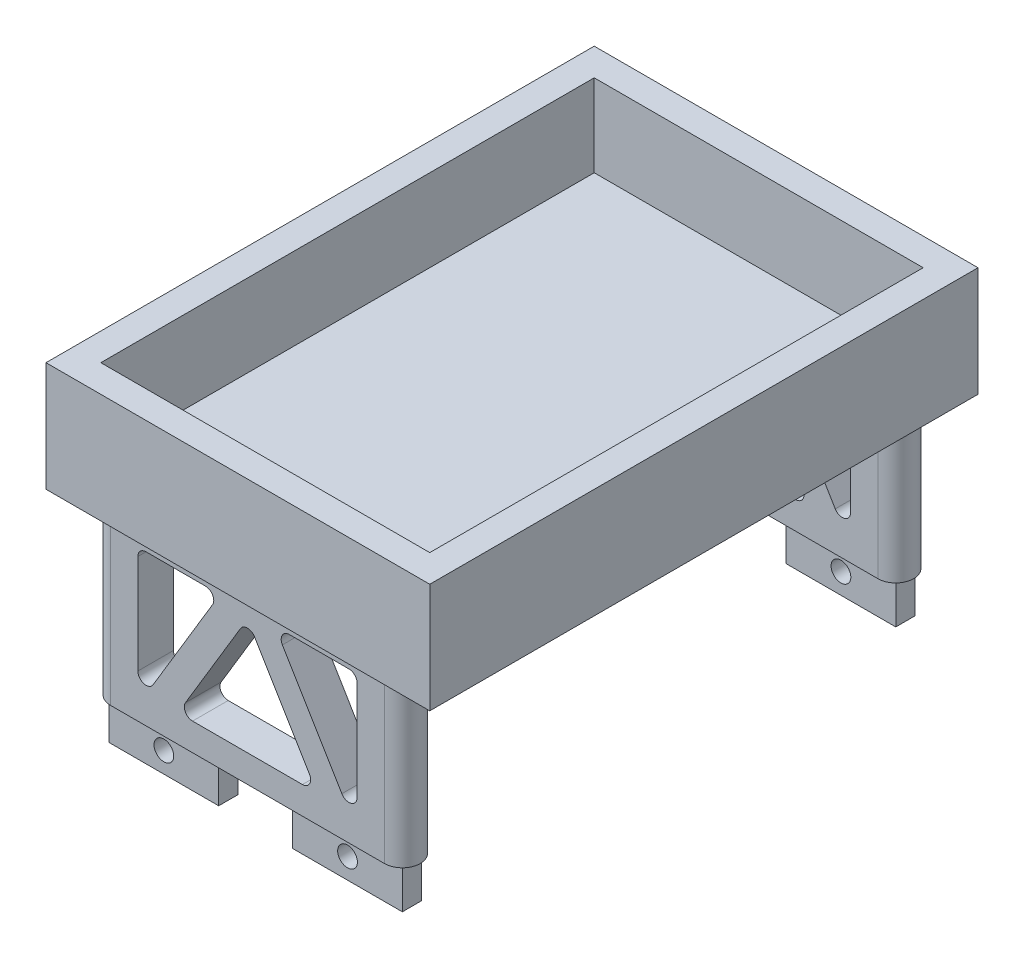
SolidWorks part; units mm, degrees
ref_plane "Front Plane" through (0, 0, 0) normal (0, 0, 1) x (1, 0, 0)
ref_plane "Top Plane" through (0, 0, 0) normal (0, 1, 0) x (1, 0, 0)
ref_plane "Right Plane" through (0, 0, 0) normal (1, 0, 0) x (0, 0, -1)
sketch "Sketch1" plane through (0, 0, 0) normal (0, 1, 0) x (1, 0, 0)
  line L0 (-52.3842, 23.5477) -> (-52.3842, -66.4523) construction
  line L1 (-2.3842, 23.5477) -> (-2.3842, -66.4523) construction
  line L2 (-52.3842, 23.5477) -> (-2.3842, 23.5477) construction
  line L3 (-52.3842, -21.4523) -> (-2.3842, -21.4523) construction
  line L4 (-54.1342, 25.2977) -> (-34.1342, 25.2977)
  line L5 (-54.1342, 25.2977) -> (-54.1342, 21.7977)
  line L6 (-54.1342, 21.7977) -> (-34.1342, 21.7977)
  line L7 (-34.1342, 25.2977) -> (-34.1342, 21.7977)
  line L8 (-0.6342, 25.2977) -> (-20.6342, 25.2977)
  line L9 (-0.6342, 25.2977) -> (-0.6342, 21.7977)
  line L10 (-0.6342, 21.7977) -> (-20.6342, 21.7977)
  line L11 (-20.6342, 25.2977) -> (-20.6342, 21.7977)
  line L13 (-54.1342, -68.2023) -> (-34.1342, -68.2023)
  line L14 (-54.1342, -68.2023) -> (-54.1342, -64.7023)
  line L15 (-54.1342, -64.7023) -> (-34.1342, -64.7023)
  line L16 (-34.1342, -68.2023) -> (-34.1342, -64.7023)
  line L17 (-0.6342, -68.2023) -> (-20.6342, -68.2023)
  line L18 (-0.6342, -68.2023) -> (-0.6342, -64.7023)
  line L19 (-0.6342, -64.7023) -> (-20.6342, -64.7023)
  line L20 (-20.6342, -68.2023) -> (-20.6342, -64.7023)
  circle A0 centre (-52.3842, 23.5477) radius 1.75 construction
  circle A1 centre (-2.3842, 23.5477) radius 1.75 construction
  circle A2 centre (-52.3842, -66.4523) radius 1.75 construction
  circle A3 centre (-2.3842, -66.4523) radius 1.75 construction
  point P29 (-52.3842, 23.5477)
  point P30 (-2.3842, 23.5477)
  point P31 (-52.3842, -66.4523)
  point P32 (-2.3842, -66.4523)
  dimension "D1" = 3.5
  dimension "D3" = 90
  dimension "D2" = 50
  dimension "D4" = 20
extrude "Boss-Extrude1" add sketch "Sketch1" along normal blind 7.5
sketch "Sketch2" plane through (0, 7.5, 0) normal (0, 1, 0) x (1, 0, 0)
  line L1 (-34.1342, 25.2977) -> (-54.1342, 25.2977) construction
  line L2 (-54.1342, 25.2977) -> (-54.1342, 21.7977) construction
  line L3 (-0.6342, 21.7977) -> (-0.6342, 25.2977) construction
  line L5 (-0.6342, 25.2977) -> (-20.6342, 25.2977) construction
  line L8 (-34.1342, -64.7023) -> (-54.1342, -64.7023) construction
  line L9 (-54.1342, -64.7023) -> (-54.1342, -68.2023) construction
  line L10 (-0.6342, -64.7023) -> (-20.6342, -64.7023) construction
  line L11 (-0.6342, -68.2023) -> (-0.6342, -64.7023) construction
  circle A0 centre (-52.3842, -66.4523) radius 3.25 construction
  circle A1 centre (-52.3842, 23.5477) radius 3.25 construction
  circle A2 centre (-2.3842, 23.5477) radius 3.25 construction
  circle A3 centre (-2.3842, -66.4523) radius 3.25
  circle A4 centre (-52.3842, 23.5477) radius 3.25
  circle A5 centre (-2.3842, 23.5477) radius 3.25
  circle A6 centre (-52.3842, -66.4523) radius 3.25
  point P31 (2.0333, -67.0433)
  dimension "D1" = 6.5
  dimension "D2" = 1.75
  dimension "D3" = 1.75
  dimension "D4" = 1.75
  dimension "D5" = 1.75
  dimension "D6" = 1.75
  dimension "D7" = 1.75
  dimension "D8" = 1.75
  dimension "D9" = 1.75
extrude "Boss-Extrude2" add sketch "Sketch2" along normal blind 30
sketch "Sketch3" plane through (0, 37.5, 0) normal (0, 1, 0) x (1, 0, 0)
  line L1 (-62.3842, 28.5477) -> (7.6158, 28.5477)
  line L2 (-62.3842, 28.5477) -> (-62.3842, -71.4523)
  line L3 (-62.3842, -71.4523) -> (7.6158, -71.4523)
  line L4 (7.6158, 28.5477) -> (7.6158, -71.4523)
  circle A3 centre (-52.3842, 23.5477) radius 3.25 construction
  circle A4 centre (-2.3842, 23.5477) radius 3.25 construction
  circle A5 centre (-2.3842, -66.4523) radius 3.25 construction
  dimension "D1" = 10
  dimension "D2" = 5
  dimension "D3" = 5
  dimension "D4" = 10
extrude "Boss-Extrude3" add sketch "Sketch3" along normal blind 20
sketch "Sketch4" plane through (0, 57.5, 0) normal (0, 1, 0) x (1, 0, 0)
  line L0 (7.6158, 28.5477) -> (-62.3842, 28.5477) construction
  line L1 (-57.3842, 23.5477) -> (2.6158, 23.5477)
  line L2 (-57.3842, 23.5477) -> (-57.3842, -66.4523)
  line L3 (-57.3842, -66.4523) -> (2.6158, -66.4523)
  line L4 (2.6158, 23.5477) -> (2.6158, -66.4523)
  line L5 (7.6158, -71.4523) -> (7.6158, 28.5477) construction
  line L6 (-62.3842, -71.4523) -> (7.6158, -71.4523) construction
  line L7 (-62.3842, 28.5477) -> (-62.3842, -71.4523) construction
  dimension "D1" = 5
  dimension "D2" = 5
  dimension "D3" = 5
  dimension "D4" = 5
extrude "Cut-Extrude1" cut sketch "Sketch4" against normal blind 15
ref_plane "Plane1" through (0, 0, 69.7023) normal (0, 0, 1) x (1, 0, 0)
sketch "Sketch5" plane through (0, 0, 69.7023) normal (0, 0, 1) x (1, 0, 0)
  line L1 (-55.6342, 7.5) -> (-49.1342, 7.5) construction
  line L6 (-47.3842, 35) -> (-32.3842, 35)
  line L7 (-32.3842, 35) -> (-47.3842, 10)
  line L8 (-47.3842, 10) -> (-47.3842, 35)
  line L9 (-27.3842, 37.5) -> (-27.3842, 5) construction
  line L10 (-7.3842, 10) -> (-7.3842, 35)
  line L11 (-22.3842, 35) -> (-7.3842, 10)
  line L12 (-7.3842, 35) -> (-22.3842, 35)
  line L14 (-27.3842, 33.6151) -> (-40.0532, 12.5)
  line L15 (-40.0532, 12.5) -> (-14.7151, 12.5)
  line L16 (-14.7151, 12.5) -> (-27.3842, 33.6151)
  line L17 (-49.1342, 37.5) -> (-55.6342, 37.5) construction
  line L18 (-52.3842, 37.5) -> (-2.3842, 37.5)
  line L19 (-52.3842, 37.5) -> (-52.3842, 7.5)
  line L20 (-52.3842, 7.5) -> (-2.3842, 7.5)
  line L21 (-2.3842, 37.5) -> (-2.3842, 7.5)
  point P20 (-52.3842, 37.5)
  dimension "D1" = 2.5
  dimension "D2" = 5
  dimension "D3" = 5
  dimension "D4" = 5
  dimension "D5" = 2.5
  dimension "D6" = 5
  dimension "D7" = 15
extrude "Boss-Extrude4" add sketch "Sketch5" against normal blind 6.5
ref_plane "Plane2" through (0, 0, 21.4523) normal (0, 0, -1) x (-1, 0, 0)
mirror "Mirror1" about plane through (0, 0, 21.4523) normal (0, 0, -1) of "Boss-Extrude4"
fillet "Fillet2" radius 1.5 18 edges at (-7.3842, 35, -23.5477) (-32.3842, 35, -23.5477) (-27.3842, 33.6151, -23.5477) (-22.3842, 35, -23.5477) (-47.3842, 35, -23.5477) (-7.3842, 10, -23.5477) (-14.7151, 12.5, -23.5477) (-47.3842, 10, -23.5477) (-40.0532, 12.5, -23.5477) (-40.0532, 12.5, 66.4523) (-14.7151, 12.5, 66.4523) (-7.3842, 10, 66.4523) (-47.3842, 10, 66.4523) (-27.3842, 33.6151, 66.4523) (-47.3842, 35, 66.4523) (-22.3842, 35, 66.4523) (-32.3842, 35, 66.4523) (-7.3842, 35, 66.4523)
sketch "Sketch7" plane through (0, 0, 68.2023) normal (0, 0, 1) x (1, 0, 0)
  line L0 (-54.1342, 3.75) -> (-34.1342, 3.75) construction
  line L1 (-54.1342, 7.5) -> (-54.1342, 0) construction
  line L2 (-34.1342, 7.5) -> (-34.1342, 0) construction
  line L3 (-44.1342, 0) -> (-44.1342, 7.5) construction
  line L4 (-54.1342, 0) -> (-34.1342, 0) construction
  line L5 (-52.3842, 7.5) -> (-2.3842, 7.5) construction
  circle A0 centre (-44.1342, 3.75) radius 1.8
  dimension "D1" = 3.6
  dimension "D2" = 3.75
  dimension "D3" = 10
  dimension "D4" = 10
extrude "Cut-Extrude2" cut sketch "Sketch7" against normal up to surface (93.5 mm away) up to face at (-44.1342, 3.75, -25.2977)
ref_plane "Plane3" through (-27.3842, 0, 0) normal (-1, 0, 0) x (0, 0, 1)
mirror "Mirror2" about plane through (-27.3842, 0, 0) normal (-1, 0, 0) of "Cut-Extrude2"
